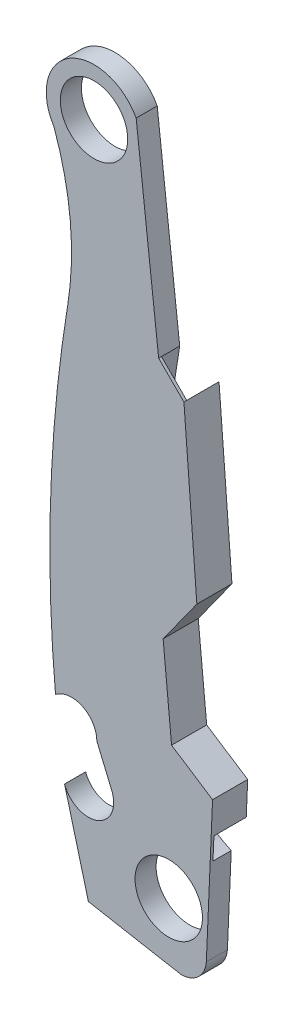
SolidWorks part; units mm, degrees
material "ABS PC"
ref_plane "Front Plane" through (0, 0, 0) normal (0, 0, 1) x (1, 0, 0)
ref_plane "Top Plane" through (0, 0, 0) normal (0, 1, 0) x (1, 0, 0)
ref_plane "Right Plane" through (0, 0, 0) normal (1, 0, 0) x (0, 0, -1)
sketch "Sketch1" plane through (0, 0, 0) normal (0, 0, 1) x (1, 0, 0)
  line L1 (-13.2319, 13.7298) -> (-15.2639, 31.5098)
  line L5 (422.6084, 1757.2346) -> (3189.852, 2048.0836) construction
  line L6 (-13.2319, 13.7298) -> (-10.9459, 11.4438)
  line L7 (-10.9459, 11.4438) -> (-9.7775, -3.7962)
  line L8 (-9.7775, -3.7962) -> (-12.8255, -8.038)
  line L9 (-12.8255, -8.038) -> (-12.0635, -15.9882)
  line L10 (-12.0635, -15.9882) -> (-8.3551, -18.4012)
  line L13 (-8.3551, -18.4012) -> (-8.9191, -31.3819)
  line L14 (-21.7372, -23.8622) -> (-19.5819, -31.9902)
  line L15 (-18.8199, -19.0362) -> (-17.5341, -22.0842)
  circle A0 centre (-19.0739, 29.4778) radius 3.048
  circle A1 centre (-12.3175, -28.104) radius 3.048
  arc A4 (-15.2639, 31.5098) -> (-22.7027, 27.1375) centre (-19.0739, 29.4778) ccw
  arc A5 (-21.4555, 13.7441) -> (-22.7027, 27.1375) centre (-47.7759, 18.0478) ccw
  arc A7 (-21.4555, 13.7441) -> (-22.5554, -17.2684) centre (99.7981, -6.0822) ccw
  arc A9 (-22.5554, -17.2684) -> (-18.8199, -19.0362) centre (-21.1059, -19.0362) cw
  arc A11 (-17.5341, -22.0842) -> (-21.7372, -23.8622) centre (-19.5819, -23.1002) cw
  arc A14 (-19.5819, -31.9902) -> (-11.1999, -33.5142) centre (206.2035, 1186.0174) ccw
  arc A17 (-8.9191, -31.3819) -> (-11.1999, -33.5142) centre (-11.1999, -31.2282) cw
  dimension "D1" = 6.096
  dimension "D2" = 4.318
  dimension "D6" = 15.748
  dimension "D7" = 5.842
  dimension "D8" = 2.032
  dimension "D10" = 8.128
  dimension "D24" = 61.468
  dimension "D27" = 48.514
  dimension "D32" = 51.562
  dimension "D33" = 48.514
  dimension "D34" = 118.872
  dimension "D5" = 26.67
  dimension "D23" = 2.286
  dimension "D29" = 2.286
  dimension "D30" = 2.286
  dimension "D37" = 1238.758
  dimension "D21" = 6.7564
  dimension "D3" = 28.702
  dimension "D4" = 11.43
  dimension "D9" = 18.034
  dimension "D11" = 33.274
  dimension "D12" = 9.2964
  dimension "D13" = 37.5158
  dimension "D14" = 6.2484
  dimension "D15" = 45.466
  dimension "D16" = 7.0104
  dimension "D17" = 47.879
  dimension "D18" = 10.7188
  dimension "D19" = 60.706
  dimension "D20" = 57.5818
  dimension "D22" = 7.874
  dimension "D25" = 0.508
  dimension "D26" = 52.578
  dimension "D28" = 2.032
  dimension "D31" = 53.34
  dimension "D35" = 35.56
  dimension "D36" = 62.992
  dimension "D38" = 10.1548
extrude "Boss-Extrude1" add sketch "Sketch1" along normal blind 1.905
sketch "Sketch5" plane through (0, 0, 1.905) normal (0, 0, 1) x (1, 0, 0)
  line L0 (-10.9459, 11.4438) -> (-13.2319, 13.7298) construction
  line L1 (-10.9459, 11.4438) -> (-13.2319, 13.7298)
  line L7 (-8.4644, -20.9151) -> (-8.5417, -22.6961)
  line L8 (-8.9191, -31.3819) -> (-8.3551, -18.4012) construction
  arc A1 (-13.3964, -2.4635) -> (-12.9035, -14.7563) centre (28.3656, -6.9451) ccw
  arc A2 (-13.3964, -2.4635) -> (-10.9459, 11.4438) centre (567.3536, -97.6231) cw
  arc A3 (-13.2319, 13.7298) -> (-15.8556, -5.8604) centre (318.9416, -40.7271) ccw
  arc A4 (-15.8556, -5.8604) -> (-12.8811, -19.1744) centre (8.2996, -7.4531) ccw
  arc A5 (-8.5417, -22.6961) -> (-12.8811, -19.1744) centre (-3.8924, -12.5331) cw
  arc A6 (-12.9035, -14.7563) -> (-8.4644, -20.9151) centre (-2.6224, -12.0251) ccw
  dimension "D1" = 8.382
  dimension "D2" = 8.89
  dimension "D3" = 13.462
  dimension "D4" = 13.97
  dimension "D5" = 19.812
  dimension "D6" = 76.708
  dimension "D13" = 42.0019
  dimension "D14" = 24.2076
  dimension "D15" = 11.176
  dimension "D7" = 4.572
  dimension "D8" = 5.842
  dimension "D9" = 16.764
  dimension "D10" = 36.83
  dimension "D11" = 327.406
  dimension "D12" = 575.818
extrude "Cut-Extrude1" [suppressed] cut sketch "Sketch5" against normal blind 1.651
sketch "Sketch6" plane through (0, 0, 1.905) normal (0, 0, 1) x (1, 0, 0)
  line L5 (-10.9459, 11.4438) -> (-13.2319, 13.7298)
  line L6 (-8.3551, -18.4012) -> (-12.0635, -15.9882)
  line L7 (-12.0635, -15.9882) -> (-12.8255, -8.038)
  line L8 (-12.8255, -8.038) -> (-9.7775, -3.7962)
  line L9 (-9.7775, -3.7962) -> (-10.9459, 11.4438)
  line L11 (-8.3551, -18.4012) -> (-12.0635, -15.9882)
  line L12 (-12.0635, -15.9882) -> (-12.8255, -8.038)
  line L13 (-12.8255, -8.038) -> (-9.7775, -3.7962)
  line L14 (-9.7775, -3.7962) -> (-10.9459, 11.4438)
  line L23 (-10.9459, 11.4438) -> (-13.2319, 13.7298)
  line L24 (-13.2319, 13.7298) -> (-15.2639, 31.5098)
  line L25 (-13.2319, 13.7298) -> (-15.2639, 31.5098)
  line L26 (-18.8199, -19.0362) -> (-17.5341, -22.0842)
  line L27 (-18.8199, -19.0362) -> (-17.5341, -22.0842)
  line L28 (-8.9191, -31.3819) -> (-8.3551, -18.4012)
  line L29 (-8.9191, -31.3819) -> (-8.3551, -18.4012)
  line L30 (-21.7372, -23.8622) -> (-19.5819, -31.9902)
  line L31 (-21.7372, -23.8622) -> (-19.5819, -31.9902)
  arc A3 (-15.2639, 31.5098) -> (-22.7027, 27.1375) centre (-19.0739, 29.4778) ccw
  arc A18 (-15.2639, 31.5098) -> (-22.7027, 27.1375) centre (-19.0739, 29.4778) ccw
  arc A22 (-21.4555, 13.7441) -> (-22.7027, 27.1375) centre (-47.7759, 18.0478) ccw
  arc A29 (-21.4555, 13.7441) -> (-22.7027, 27.1375) centre (-47.7759, 18.0478) ccw
  arc A30 (-21.4555, 13.7441) -> (-22.5554, -17.2684) centre (99.7981, -6.0822) ccw
  arc A31 (-21.4555, 13.7441) -> (-22.5554, -17.2684) centre (99.7981, -6.0822) ccw
  arc A32 (-18.8199, -19.0362) -> (-22.5554, -17.2684) centre (-21.1059, -19.0362) ccw
  arc A33 (-18.8199, -19.0362) -> (-22.5554, -17.2684) centre (-21.1059, -19.0362) ccw
  arc A34 (-21.7372, -23.8622) -> (-17.5341, -22.0842) centre (-19.5819, -23.1002) ccw
  arc A35 (-21.7372, -23.8622) -> (-17.5341, -22.0842) centre (-19.5819, -23.1002) ccw
  arc A36 (-19.5819, -31.9902) -> (-11.1999, -33.5142) centre (206.2035, 1186.0174) ccw
  arc A37 (-19.5819, -31.9902) -> (-11.1999, -33.5142) centre (206.2035, 1186.0174) ccw
  arc A38 (-11.1999, -33.5142) -> (-8.9191, -31.3819) centre (-11.1999, -31.2282) ccw
  arc A39 (-11.1999, -33.5142) -> (-8.9191, -31.3819) centre (-11.1999, -31.2282) ccw
  dimension "D1" = 0
extrude "Boss-Extrude2" [suppressed] add sketch "Sketch6" along normal blind 1.27
sketch "Sketch7" plane through (0, 0, 0) normal (0, 0, 1) x (1, 0, 0)
  line L0 (-10.9459, 11.4438) -> (-13.2319, 13.7298)
  line L1 (-8.4865, -21.4258) -> (-8.5743, -23.4445)
  line L2 (-8.9191, -31.3819) -> (-8.3551, -18.4012) construction
  arc A0 (-13.6281, -3.7756) -> (-12.8867, -15.2834) centre (28.4241, -6.8442) ccw
  arc A1 (-13.6281, -3.7756) -> (-10.9459, 11.4438) centre (567.1581, -98.2842) cw
  arc A2 (-13.2319, 13.7298) -> (-16.0259, -7.4446) centre (319.0001, -40.8802) ccw
  arc A3 (-16.0259, -7.4446) -> (-11.6695, -21.3654) centre (8.3581, -7.4558) ccw
  arc A4 (-8.5743, -23.4445) -> (-11.6695, -21.3654) centre (-3.8339, -13.0438) cw
  arc A5 (-12.8867, -15.2834) -> (-8.4865, -21.4258) centre (-2.5639, -12.5358) ccw
  dimension "D15" = 24.384
  dimension "D16" = 42.164
  dimension "D17" = 11.43
  dimension "D18" = 10.6822
  dimension "D1" = 2.286
  dimension "D2" = 2.286
  dimension "D3" = 8.382
  dimension "D4" = 8.89
  dimension "D5" = 13.97
  dimension "D6" = 18.288
  dimension "D7" = 52.324
  dimension "D8" = 109.728
  dimension "D9" = 7.112
  dimension "D10" = 8.382
  dimension "D11" = 19.304
  dimension "D12" = 39.37
  dimension "D13" = 329.946
  dimension "D14" = 578.104
extrude "Cut-Extrude2" cut sketch "Sketch7" along normal blind 1.651
sketch "Sketch8" plane through (0, 0, 0) normal (0, 0, -1) x (-1, 0, 0)
  line L5 (8.3551, -18.4012) -> (8.4865, -21.4258)
  line L6 (10.9459, 11.4438) -> (9.7775, -3.7962)
  line L7 (9.7775, -3.7962) -> (12.8255, -8.038)
  line L8 (12.8255, -8.038) -> (12.0635, -15.9882)
  line L9 (12.0635, -15.9882) -> (8.3551, -18.4012)
  line L10 (8.3551, -18.4012) -> (8.4865, -21.4258)
  line L11 (10.9459, 11.4438) -> (9.7775, -3.7962)
  line L12 (9.7775, -3.7962) -> (12.8255, -8.038)
  line L13 (12.8255, -8.038) -> (12.0635, -15.9882)
  line L14 (12.0635, -15.9882) -> (8.3551, -18.4012)
  arc A3 (8.4865, -21.4258) -> (12.8867, -15.2834) centre (2.5639, -12.5358) ccw
  arc A4 (12.8867, -15.2834) -> (13.6281, -3.7756) centre (-28.4241, -6.8442) ccw
  arc A5 (13.6281, -3.7756) -> (10.9459, 11.4438) centre (-567.1581, -98.2842) ccw
  arc A6 (8.4865, -21.4258) -> (12.8867, -15.2834) centre (2.5639, -12.5358) ccw
  arc A7 (12.8867, -15.2834) -> (13.6281, -3.7756) centre (-28.4241, -6.8442) ccw
  arc A8 (13.6281, -3.7756) -> (10.9459, 11.4438) centre (-567.1581, -98.2842) ccw
  dimension "D1" = 0
extrude "Boss-Extrude3" add sketch "Sketch8" along normal blind 1.27
